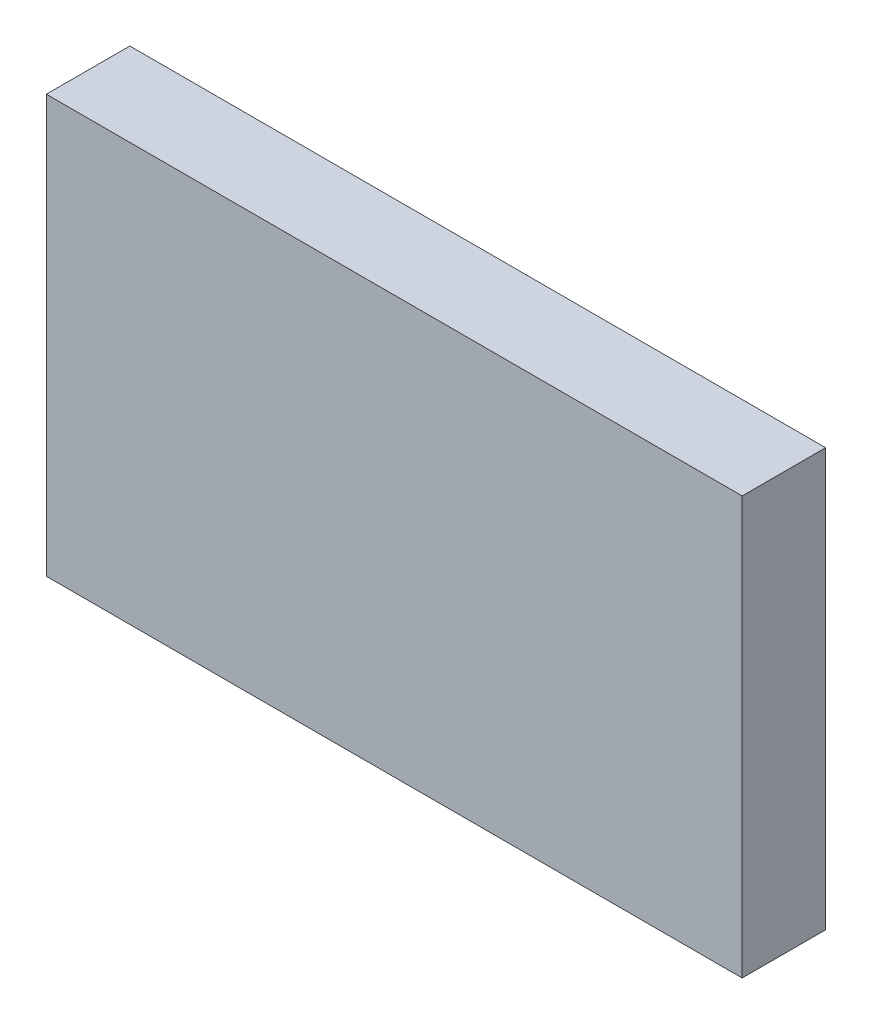
SolidWorks part; units mm, degrees
ref_plane "Front Plane" through (0, 0, 0) normal (0, 0, 1) x (1, 0, 0)
ref_plane "Top Plane" through (0, 0, 0) normal (0, 1, 0) x (1, 0, 0)
ref_plane "Right Plane" through (0, 0, 0) normal (1, 0, 0) x (0, 0, -1)
sketch "Model" plane through (0, 0, 0) normal (0, 0, 1) x (1, 0, 0)
  line L0 (64.6035, 37.0448) -> (64.6035, 7.0448)
  line L1 (64.6035, 7.0448) -> (14.6035, 7.0448)
  line L2 (14.6035, 7.0448) -> (14.6035, 37.0448)
  line L3 (14.6035, 37.0448) -> (64.6035, 37.0448)
extrude "Boss-Extrude1" add sketch "Model" along normal blind 6 contours L2 L3 L0 L1
